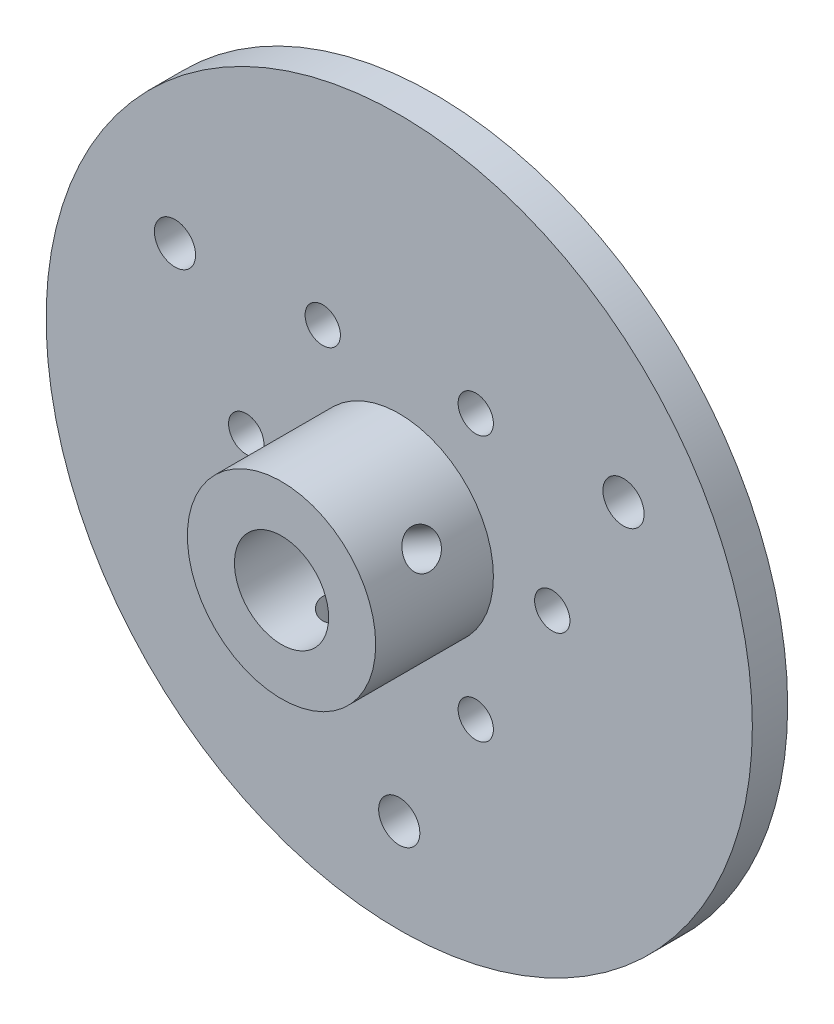
SolidWorks part; units mm, degrees
material "1060 Alloy"
ref_plane "Front Plane" through (0, 0, 0) normal (0, 0, 1) x (1, 0, 0)
ref_plane "Top Plane" through (0, 0, 0) normal (0, 1, 0) x (1, 0, 0)
ref_plane "Right Plane" through (0, 0, 0) normal (1, 0, 0) x (0, 0, -1)
sketch "Sketch2" plane through (0, 0, 0) normal (0, 0, 1) x (1, 0, 0)
  circle A0 centre (0, 0) radius 4
  circle A2 centre (0, 0) radius 22 construction
  circle A3 centre (0, 0) radius 30
  circle A4 centre (0, -22) radius 1.75
  circle A5 centre (-19.0526, 11) radius 1.75
  circle A6 centre (19.0526, 11) radius 1.75
  point P13 (0, 0)
  dimension "D1" = 3
  dimension "D2" = 44
  dimension "D3" = 3.5
  dimension "D4" = 8
  dimension "D5" = 60
extrude "Boss-Extrude1" add sketch "Sketch2" along normal blind 3
sketch "Sketch3" plane through (0, 0, 3) normal (0, 0, 1) x (1, 0, 0)
  circle A0 centre (0, 0) radius 8
  circle A1 centre (0, 0) radius 4
  dimension "D1" = 16
  dimension "D2" = 8
extrude "Boss-Extrude2" add sketch "Sketch3" along normal blind 10
sketch "Sketch4" plane through (0, 0, 3) normal (0, 0, 1) x (1, 0, 0)
  line L0 (0, 0) -> (-17.8949, 30.9948) construction
  line L1 (0, 0) -> (0, 33.1815) construction
  line L2 (0, 0) -> (16.5859, 28.7276) construction
  circle A9 centre (0, 0) radius 13
  circle A10 centre (-6.5, 11.2583) radius 1.5
  circle A11 centre (13, 0) radius 1.5
  circle A12 centre (-6.5, -11.2583) radius 1.5
  circle A14 centre (6.5, 11.2583) radius 1.5
  circle A15 centre (6.5, -11.2583) radius 1.5
  circle A16 centre (-13, 0) radius 1.5
  point P11 (0, 0)
  point P12 (0, 0)
  point P13 (0, 0)
  point P24 (0, 0)
  dimension "D1" = 3
  dimension "D2" = 3
  dimension "D4" = 26
  dimension "D3" = 30
  dimension "D5" = 2
  dimension "D6" = 30
extrude "Cut-Extrude2" cut sketch "Sketch4" against normal through all contours A12 | A11 | A10 | A16 | A14 | A15
sketch "Sketch12" plane through (0, 0, 0) normal (0, 1, 0) x (1, 0, 0)
  circle A0 centre (0, -8) radius 1.5
  dimension "D1" = 3
  dimension "D2" = 8
extrude "Cut-Extrude3" cut sketch "Sketch12" against normal blind 11.4938
pattern_circular "CirPattern1" count 3 every 120 of "Cut-Extrude3"
